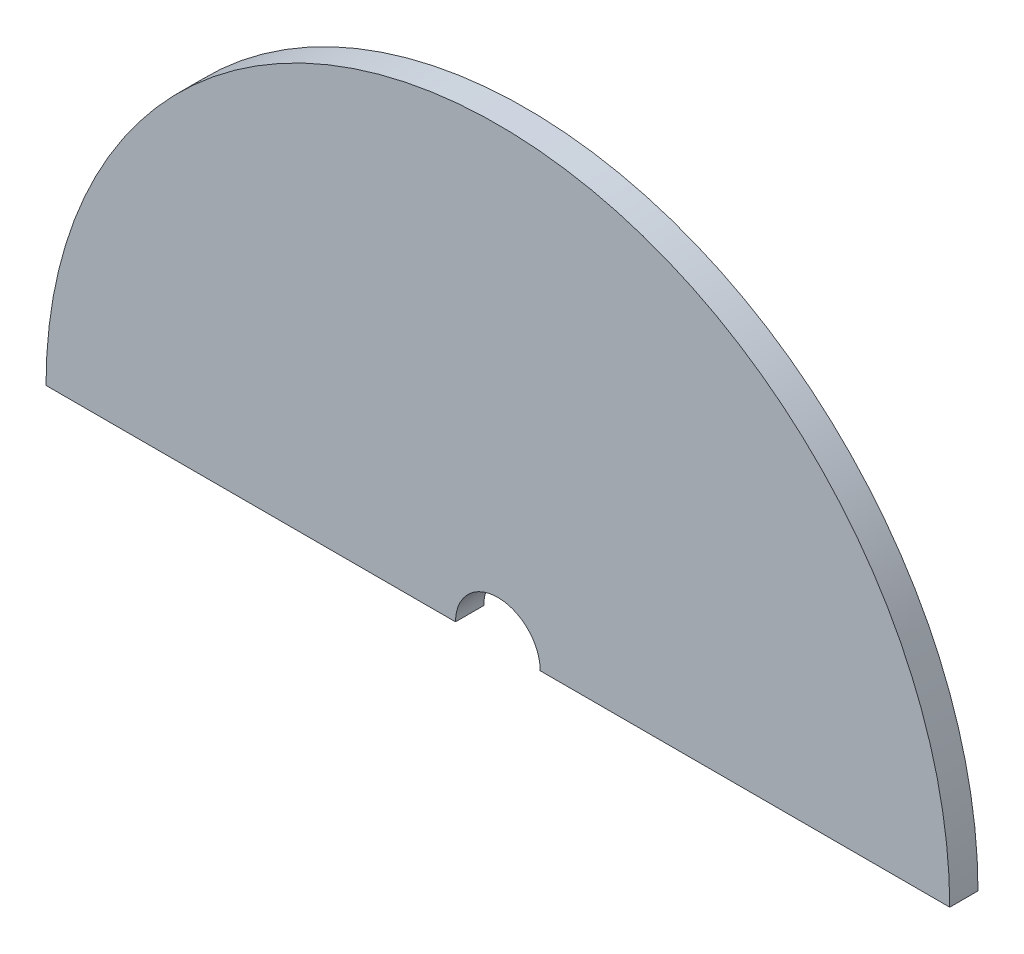
SolidWorks part; units mm, degrees
material "201 Annealed Stainless Steel (SS)"
ref_plane "Front Plane" through (0, 0, 0) normal (0, 0, 1) x (1, 0, 0)
ref_plane "Top Plane" through (0, 0, 0) normal (0, 1, 0) x (1, 0, 0)
ref_plane "Right Plane" through (0, 0, 0) normal (1, 0, 0) x (0, 0, -1)
sketch "Plate shape" plane through (0, 0, 0) normal (0, 0, 1) x (1, 0, 0)
  line L3 (-154.3999, 0) -> (210.7061, 0) construction
  line L4 (0, 160) -> (-160, 160)
  line L5 (0, 160) -> (160, 160)
  line L9 (0, 160) -> (0, 0) construction
  line L10 (0, 160) -> (30, 160) construction
  line L11 (30, 160) -> (30, 317.1623) construction
  arc A0 (-160, 160) -> (160, 160) centre (0, 160) cw
  arc A1 (160, 160) -> (-160, 160) centre (0, 160) cw construction
  dimension "D1" = 160
  dimension "D2" = 30
extrude "Outer casing" add sketch "Plate shape" along normal blind 10
sketch "Sketch1" plane through (0, 0, 10) normal (0, 0, 1) x (1, 0, 0)
  circle A0 centre (0, 160) radius 160 construction
  arc A1 (160, 160) -> (-160, 160) centre (0, 160) ccw construction
  circle A2 centre (0, 160) radius 15
  dimension "D1" = 30
extrude "Inner Cutout" cut sketch "Sketch1" against normal blind 20
sketch "Sketch3" plane through (0, 0, 10) normal (0, 0, 1) x (1, 0, 0)
  line L0 (30, 160) -> (30, 317.1623) construction
  line L1 (15, 160) -> (160, 160) construction
  line L2 (-15, 160) -> (15, 160) construction
  arc A0 (160, 160) -> (-160, 160) centre (0, 160) ccw construction
  point P11 (0, 160)
  dimension "D1" = 30
